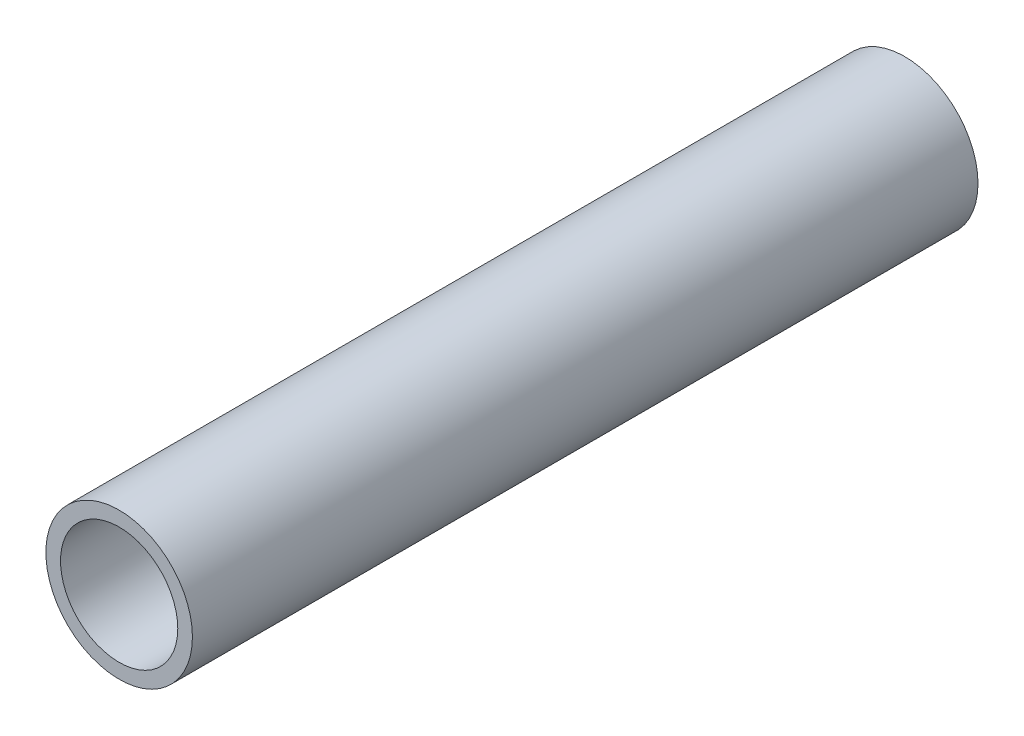
SolidWorks part; units mm, degrees
material "Bronce de aluminio"
ref_plane "Alzado" through (0, 0, 0) normal (0, 0, 1) x (1, 0, 0)
ref_plane "Planta" through (0, 0, 0) normal (0, 1, 0) x (1, 0, 0)
ref_plane "Vista lateral" through (0, 0, 0) normal (1, 0, 0) x (0, 0, -1)
sketch "Croquis2" plane through (0, 0, 0) normal (0, 0, 1) x (1, 0, 0)
  circle A0 centre (0, 0) radius 43.75
  dimension "D1" = 87.5
extrude "Saliente-Extruir8" add sketch "Croquis2" along normal blind 469
sketch "Croquis4" plane through (0, 0, 469) normal (0, 0, 1) x (1, 0, 0)
  circle A0 centre (0, 0) radius 35
  dimension "D1" = 70
extrude "Cortar-Extruir1" cut sketch "Croquis4" against normal blind 462
